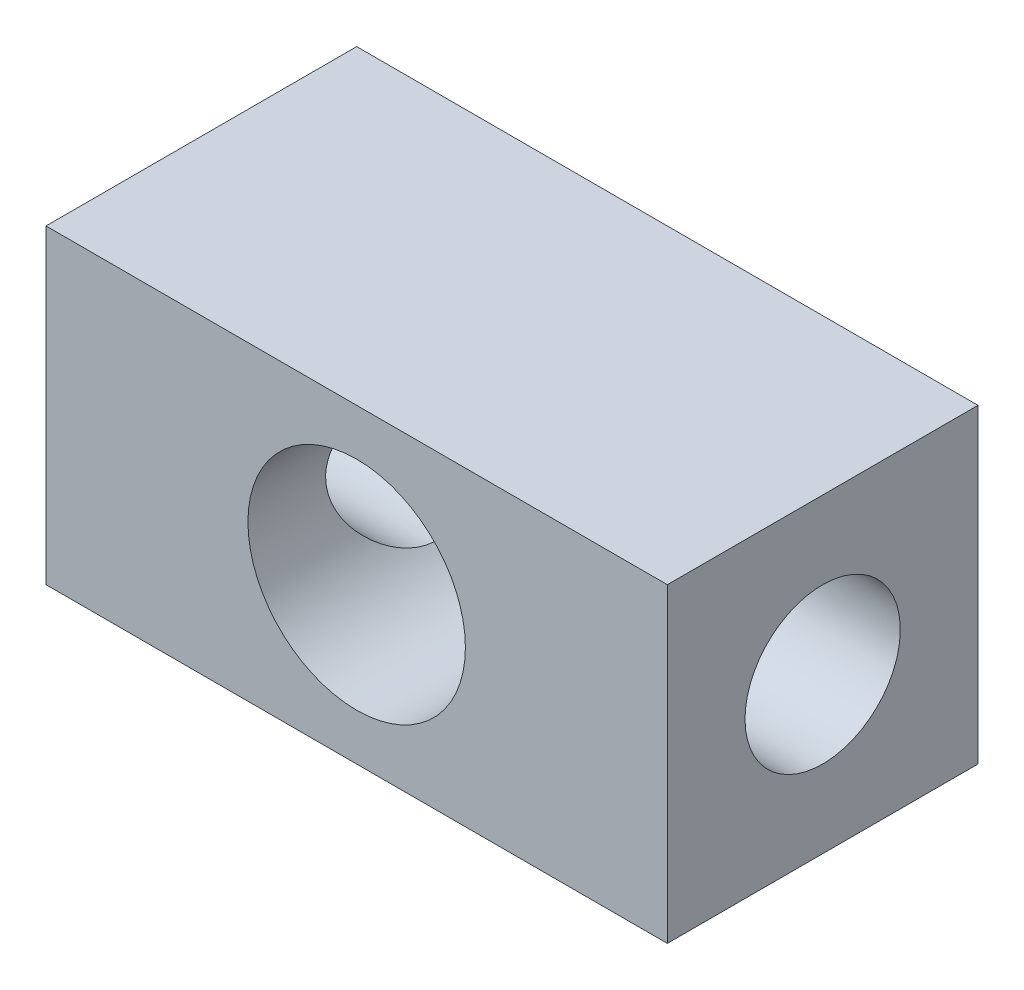
SolidWorks part; units mm, degrees
ref_plane "前视基准面" through (0, 0, 0) normal (0, 0, 1) x (1, 0, 0)
ref_plane "上视基准面" through (0, 0, 0) normal (0, 1, 0) x (1, 0, 0)
ref_plane "右视基准面" through (0, 0, 0) normal (1, 0, 0) x (0, 0, -1)
other "Configuration Table"
sketch "草图1" plane through (0, 0, 0) normal (0, 0, 1) x (1, 0, 0)
  line L1 (-20, -10) -> (20, -10)
  line L2 (-20, -10) -> (-20, 10)
  line L3 (-20, 10) -> (20, 10)
  line L4 (20, -10) -> (20, 10)
  line L5 (-20, -10) -> (20, 10) construction
  line L6 (-20, 10) -> (20, -10) construction
  circle A0 centre (0, 0) radius 7
  point P0 (0, 0)
  dimension "D3" = 14
  dimension "D1" = 40
  dimension "D2" = 20
extrude "凸台-拉伸1" add sketch "草图1" along normal blind 20
sketch "草图2" plane through (-20, 0, 0) normal (-1, 0, 0) x (0, 0, 1)
  line L0 (20, 10) -> (0, 10) construction
  line L2 (20, 10) -> (20, -10) construction
  circle A0 centre (10, 0) radius 5
  dimension "D1" = 10
  dimension "D2" = 10
  dimension "D3" = 10
extrude "切除-拉伸1" cut sketch "草图2" against normal through all
